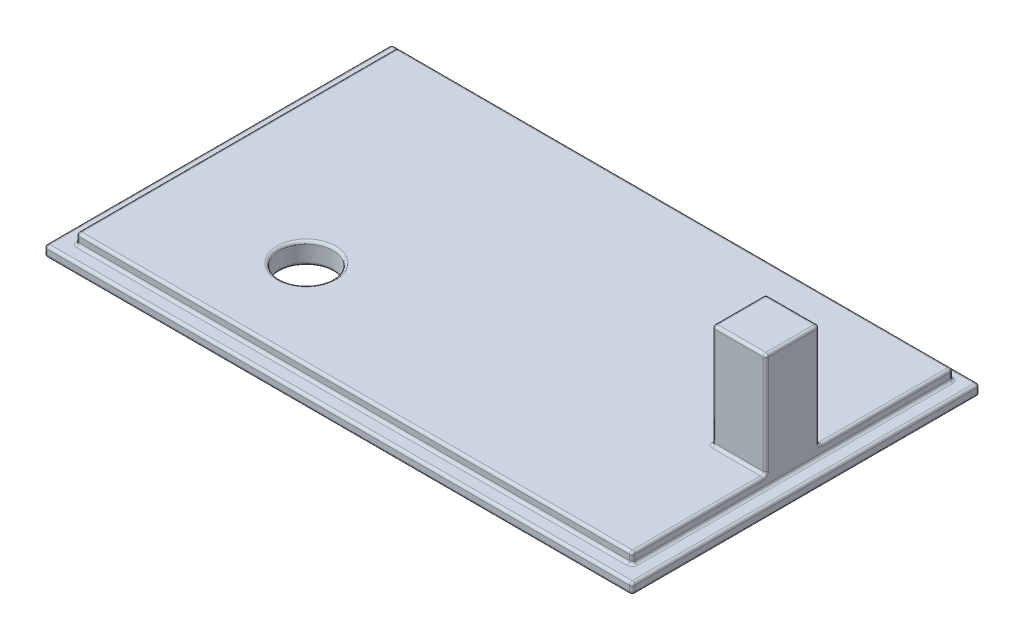
SolidWorks part; units mm, degrees
ref_plane "Front Plane" through (0, 0, 0) normal (0, 0, 1) x (1, 0, 0)
ref_plane "Top Plane" through (0, 0, 0) normal (0, 1, 0) x (1, 0, 0)
ref_plane "Right Plane" through (0, 0, 0) normal (1, 0, 0) x (0, 0, -1)
sketch "Sketch1" plane through (0, 0, 0) normal (0, 1, 0) x (1, 0, 0)
  line L1 (-57.9549, 34.3335) -> (52.0451, 34.3335)
  line L2 (-57.9549, 34.3335) -> (-57.9549, -30.6665)
  line L3 (-57.9549, -30.6665) -> (52.0451, -30.6665)
  line L4 (52.0451, 34.3335) -> (52.0451, -30.6665)
  dimension "D1" = 110
  dimension "D2" = 65
extrude "Boss-Extrude1" add sketch "Sketch1" along normal blind 2
sketch "Sketch2" plane through (0, 2, 0) normal (0, 1, 0) x (1, 0, 0)
  line L0 (-57.9549, 34.3335) -> (-57.9549, -30.6665) construction
  line L1 (-54.9549, 32.3335) -> (49.0451, 32.3335)
  line L2 (-54.9549, 32.3335) -> (-54.9549, -27.6665)
  line L3 (-54.9549, -27.6665) -> (49.0451, -27.6665)
  line L4 (49.0451, 32.3335) -> (49.0451, -27.6665)
  line L5 (-57.9549, -30.6665) -> (52.0451, -30.6665) construction
  line L6 (52.0451, -30.6665) -> (52.0451, 34.3335) construction
  line L7 (52.0451, 34.3335) -> (-57.9549, 34.3335) construction
  dimension "D1" = 3
  dimension "D2" = 3
  dimension "D3" = 3
  dimension "D4" = 2
extrude "Boss-Extrude3" add sketch "Sketch2" along normal blind 2 contours L2 L3 L4 L1
sketch "Sketch6" plane through (0, 4, 0) normal (0, 1, 0) x (1, 0, 0)
  line L0 (49.0451, 32.3335) -> (49.0451, -27.6665) construction
  line L1 (49.0451, 7.3335) -> (39.0451, 7.3335)
  line L2 (49.0451, 7.3335) -> (49.0451, -2.6665)
  line L3 (49.0451, -2.6665) -> (39.0451, -2.6665)
  line L4 (39.0451, 7.3335) -> (39.0451, -2.6665)
  line L8 (-54.9549, -27.6665) -> (49.0451, -27.6665) construction
  dimension "D1" = 10
  dimension "D2" = 10
  dimension "D3" = 25
extrude "Boss-Extrude4" add sketch "Sketch6" along normal blind 19.5 contours L3 L4 L1 L2
sketch "Sketch7" plane through (0, 4, 0) normal (0, 1, 0) x (1, 0, 0)
  line L0 (-54.9549, 32.3335) -> (-54.9549, -27.6665) construction
  line L1 (-54.9549, -27.6665) -> (49.0451, -27.6665) construction
  circle A0 centre (-28.4549, -11.1665) radius 5
  dimension "D3" = 10
  dimension "D1" = 26.5
  dimension "D2" = 16.5
extrude "Cut-Extrude1" cut sketch "Sketch7" against normal through all
fillet "Fillet1" radius 0.5 38 edges at (-2.9549, 0, -34.3335) (-2.9549, 2, -32.3335) (-2.9549, 2, -34.3335) (-2.9549, 4, -32.3335) (-57.9549, 1, -34.3335) (-57.9549, 2, -1.8335) (-57.9549, 0, -1.8335) (-54.9549, 3, -32.3335) (-54.9549, 4, -2.3335) (-54.9549, 2, -2.3335) (39.0451, 4, -2.3335) (39.0451, 13.75, -7.3335) (44.0451, 4, -7.3335) (39.0451, 23.5, -2.3335) (44.0451, 23.5, -7.3335) (-28.4549, 4, 16.1665) (-28.4549, 0, 16.1665) (-57.9549, 1, 30.6665) (-2.9549, 2, 30.6665) (-2.9549, 0, 30.6665) (52.0451, 1, 30.6665) (52.0451, 2, -1.8335) (52.0451, 1, -34.3335) (52.0451, 0, -1.8335) (-54.9549, 3, 27.6665) (-2.9549, 4, 27.6665) (-2.9549, 2, 27.6665) (49.0451, 3, 27.6665) (49.0451, 4, 15.1665) (49.0451, 23.5, -2.3335) (49.0451, 13.75, -7.3335) (49.0451, 4, -19.8335) (49.0451, 3, -32.3335) (49.0451, 2, -2.3335) (39.0451, 13.75, 2.6665) (44.0451, 23.5, 2.6665) (49.0451, 13.75, 2.6665) (44.0451, 4, 2.6665)
equation "\"boxlengthout\"=180"
equation "\"boxwidthout\"= 120"
equation "\"board_arduinoheight\"= 24"
equation "\"boardwidth\"= 60"
equation "\"boardlength\"= 77"
equation "\"batterylength\"= 48"
equation "\"batterywidth\"= 25"
equation "\"batteryheight\"= 15"
equation "\"boxthickenss\"= 2"
equation "\"dividerheight\"=5"
equation "\"D1@Sketch1\"=\"boardlength\"+\"batterywidth\"+3*\"boxthickenss\"+2"
equation "\"D2@Sketch1\"=\"boardwidth\"+\"boxthickenss\"*2+1"
equation "\"D1@Boss-Extrude1\"=\"boxthickenss\""
equation "\"D1@Sketch2\"=\"lid_separation\""
equation "\"lid_separation\"= 3"
equation "\"D2@Sketch2\"=\"lid_separation\""
equation "\"D3@Sketch2\"=\"lid_separation\""
equation "\"lid_depth\"= 2"
equation "\"D1@Boss-Extrude3\"=\"lid_depth\""
equation "\"battery_to_top\"= 19.5"
equation "\"spacer_dim\"= 10"
equation "\"D1@Sketch6\"=\"spacer_dim\""
equation "\"D2@Sketch6\"=\"spacer_dim\""
equation "\"D3@Sketch6\"=(\"RD1@Annotations\"-\"D2@Sketch6\")/2"
equation "\"D1@Boss-Extrude4\"=\"battery_to_top\""
equation "\"short_to_battery\"=26.5"
equation "\"long_to_battery\"= 17"
equation "\"battery_hole\"= 10"
equation "\"D1@Sketch7\"=\"short_to_battery\""
